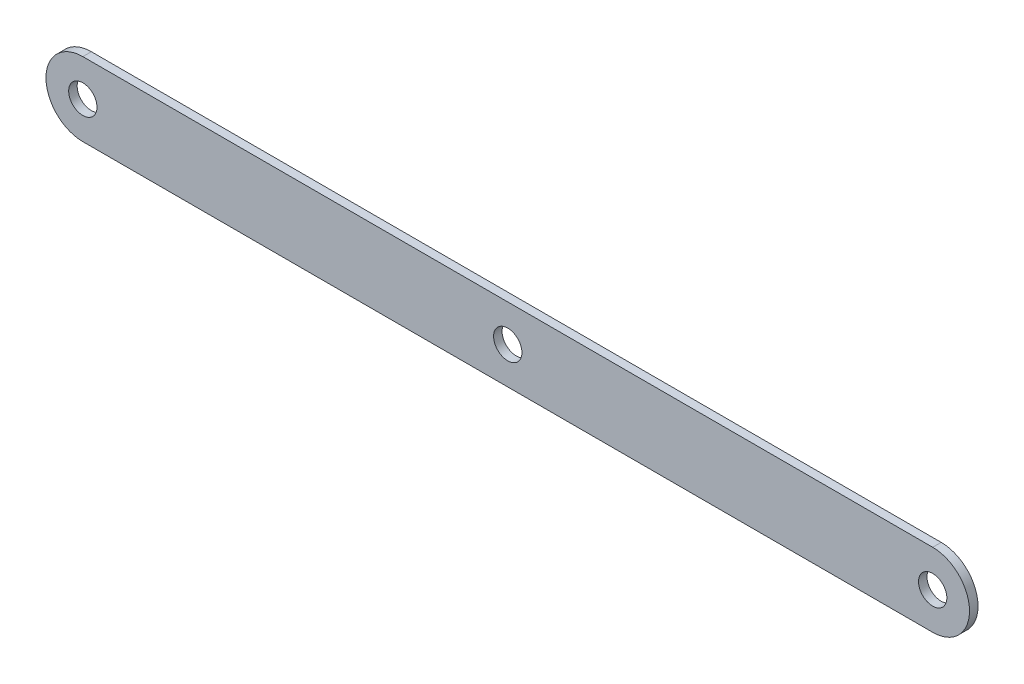
SolidWorks part; units mm, degrees
ref_plane "Front Plane" through (0, 0, 0) normal (0, 0, 1) x (1, 0, 0)
ref_plane "Top Plane" through (0, 0, 0) normal (0, 1, 0) x (1, 0, 0)
ref_plane "Right Plane" through (0, 0, 0) normal (1, 0, 0) x (0, 0, -1)
sketch "Sketch1" plane through (0, 0, 0) normal (0, 0, 1) x (1, 0, 0)
  line L0 (8.0573, 0.2349) -> (8.0573, -35.8998) construction
  line L1 (-66.9427, 0.2349) -> (83.0573, 0.2349)
  line L3 (-66.9427, -12.7651) -> (83.0573, -12.7651)
  arc A0 (83.0573, 0.2349) -> (83.0573, -12.7651) centre (83.0573, -6.2651) cw
  arc A1 (-66.9427, 0.2349) -> (-66.9427, -12.7651) centre (-66.9427, -6.2651) ccw
  circle A2 centre (-66.9427, -6.2651) radius 2.5
  circle A3 centre (83.0573, -6.2651) radius 2.5
  circle A4 centre (8.0573, -6.2651) radius 2.5
  dimension "D3" = 5
  dimension "D4" = 5
  dimension "D5" = 5
  dimension "D1" = 13
  dimension "D2" = 150
extrude "Boss-Extrude1" add sketch "Sketch1" along normal blind 1.5
